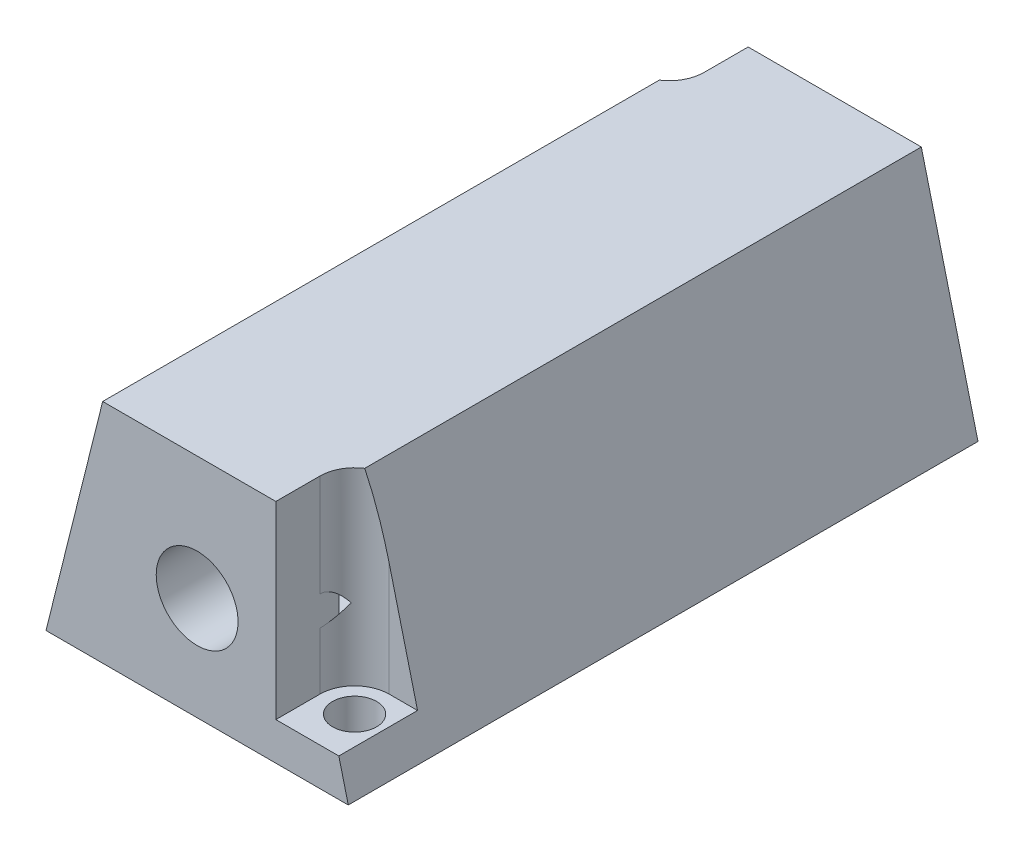
SolidWorks part; units mm, degrees
ref_plane "Alzado" through (0, 0, 0) normal (0, 0, 1) x (1, 0, 0)
ref_plane "Planta" through (0, 0, 0) normal (0, 1, 0) x (1, 0, 0)
ref_plane "Vista lateral" through (0, 0, 0) normal (1, 0, 0) x (0, 0, -1)
sketch "Croquis1" plane through (0, 0, 0) normal (0, 0, 1) x (1, 0, 0)
  line L0 (-11.14, 4.3511) -> (12.86, 4.3511)
  line L1 (12.86, 4.3511) -> (8.36, 22.3511)
  line L2 (8.36, 22.3511) -> (-6.64, 22.3511)
  line L3 (-6.64, 22.3511) -> (-11.14, 4.3511)
  line L4 (0.86, 22.3511) -> (0.86, 13.0649) construction
  line L6 (-6.0682, 13.0649) -> (-2.6041, 7.0649)
  line L7 (-2.6041, 7.0649) -> (4.3241, 7.0649)
  line L8 (4.3241, 7.0649) -> (7.7882, 13.0649)
  line L9 (7.7882, 13.0649) -> (4.3241, 19.0649)
  line L10 (4.3241, 19.0649) -> (-2.6041, 19.0649)
  line L11 (-2.6041, 19.0649) -> (-6.0682, 13.0649)
  circle A0 centre (0.86, 13.0649) radius 6 construction
  dimension "D5" = 12
  dimension "D1" = 24
  dimension "D2" = 18
  dimension "D3" = 15
  dimension "D4" = 12
extrude "Saliente-Extruir1" add sketch "Croquis1" along normal blind 50
sketch "Croquis3" plane through (0, 4.3511, 0) normal (0, -1, 0) x (1, 0, 0)
  line L4 (-11.14, 50) -> (12.86, 50) construction
  line L5 (12.86, 50) -> (12.86, 0) construction
  line L6 (-11.14, 50) -> (-11.14, 0) construction
  line L7 (-11.14, 0) -> (12.86, 0) construction
  circle A2 centre (-8.14, 3.5) radius 1.75
  circle A3 centre (9.86, 46.5) radius 1.75
  dimension "D1" = 3.5
  dimension "D2" = 3.5
  dimension "D3" = 3
  dimension "D4" = 3.5
  dimension "D6" = 3.5
  dimension "D5" = 3
extrude "Cortar-Extruir1" cut sketch "Croquis3" against normal blind 50
ref_plane "Plano1" through (0, 7.3511, 0) normal (0, -1, 0) x (-1, 0, 0)
sketch "Croquis4" plane through (0, 7.3511, 0) normal (0, -1, 0) x (-1, 0, 0)
  line L10 (-18.11, -43.75) -> (-9.86, -43.75)
  line L11 (-18.11, -54.75) -> (-18.11, -43.75)
  line L12 (-7.11, -54.75) -> (-18.11, -54.75)
  line L13 (-7.11, -46.5) -> (-7.11, -54.75)
  line L14 (16.39, -6.25) -> (8.14, -6.25)
  line L15 (16.39, 4.75) -> (16.39, -6.25)
  line L16 (5.39, 4.75) -> (16.39, 4.75)
  line L17 (5.39, -3.5) -> (5.39, 4.75)
  circle A0 centre (-9.86, -46.5) radius 1.75 construction
  circle A1 centre (8.14, -3.5) radius 1.75 construction
  arc A2 (-9.86, -43.75) -> (-7.11, -46.5) centre (-9.86, -46.5) cw
  arc A3 (8.14, -6.25) -> (5.39, -3.5) centre (8.14, -3.5) cw
  dimension "D1" = 1
  dimension "D2" = 11
  dimension "D4" = 1
  dimension "D3" = 11
  dimension "D5" = 11
  dimension "D6" = 11
extrude "Cortar-Extruir2" cut sketch "Croquis4" against normal blind 50
sketch "Croquis5" plane through (0, 0, 50) normal (0, 0, 1) x (1, 0, 0)
  line L1 (7.11, 22.3511) -> (-6.64, 22.3511)
  line L2 (7.11, 22.3511) -> (7.11, 6.6825)
  line L3 (7.11, 6.6825) -> (-6.64, 6.6825)
  line L4 (-6.64, 22.3511) -> (-6.64, 6.6825)
extrude "Saliente-Extruir2" add sketch "Croquis5" against normal blind 5
sketch "Croquis6" plane through (0, 0, 0) normal (0, 0, -1) x (-1, 0, 0)
  circle A0 centre (-0.86, 12.5649) radius 3.25
  dimension "D1" = 6.5
extrude "Cortar-Extruir3" cut sketch "Croquis6" against normal through all
